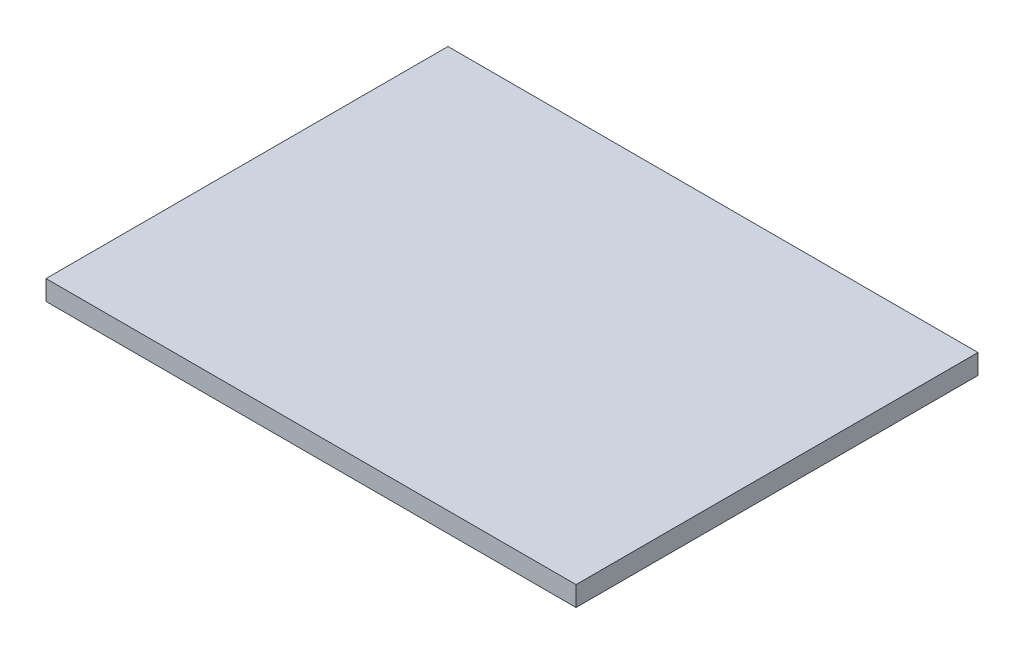
SolidWorks part; units mm, degrees
ref_plane "Front Plane" through (0, 0, 0) normal (0, 0, 1) x (1, 0, 0)
ref_plane "Top Plane" through (0, 0, 0) normal (0, 1, 0) x (1, 0, 0)
ref_plane "Right Plane" through (0, 0, 0) normal (1, 0, 0) x (0, 0, -1)
sketch "Sketch1" plane through (0, 0, 0) normal (0, 1, 0) x (1, 0, 0)
  line L1 (441.5756, -17.0557) -> (-38.4244, -17.0557)
  line L2 (441.5756, -17.0557) -> (441.5756, 346.9443)
  line L3 (441.5756, 346.9443) -> (-38.4244, 346.9443)
  line L4 (-38.4244, -17.0557) -> (-38.4244, 346.9443)
  dimension "D1" = 364
  dimension "D2" = 480
extrude "Boss-Extrude1" add sketch "Sketch1" along normal blind 18
